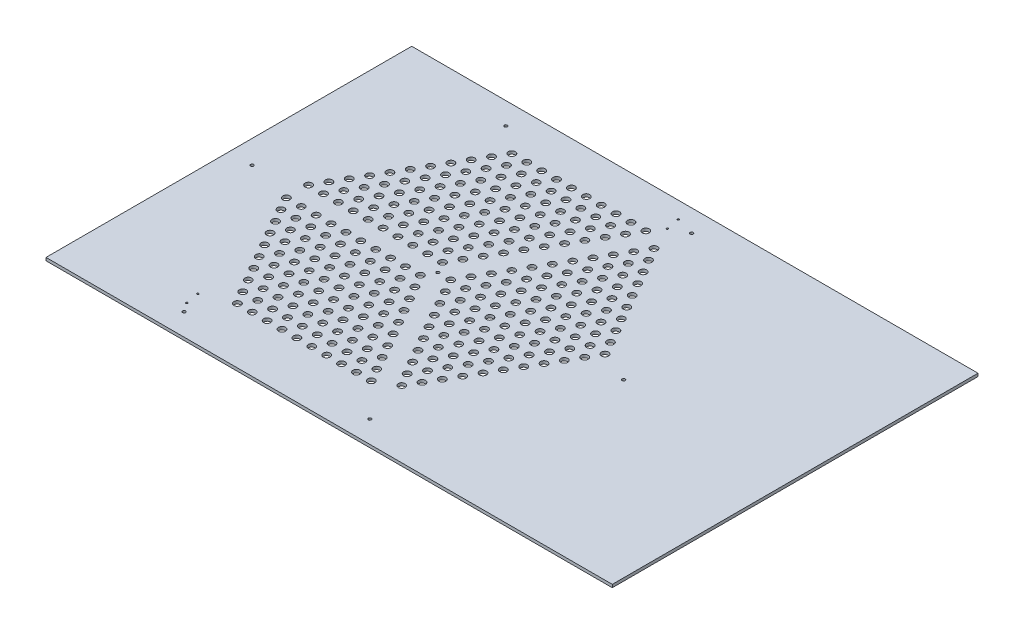
SolidWorks part; units mm, degrees
material "Oak"
ref_plane "Front Plane" through (0, 0, 0) normal (0, 0, 1) x (1, 0, 0)
ref_plane "Top Plane" through (0, 0, 0) normal (0, 1, 0) x (1, 0, 0)
ref_plane "Right Plane" through (0, 0, 0) normal (1, 0, 0) x (0, 0, -1)
sketch "Sketch1" plane through (0, 0, 0) normal (0, 1, 0) x (1, 0, 0)
  line L7 (-450, 393.7) -> (769.2, 393.7)
  line L8 (-450, 393.7) -> (-450, -393.7)
  line L9 (-450, -393.7) -> (769.2, -393.7)
  line L10 (769.2, 393.7) -> (769.2, -393.7)
  point P0 (-450, 0)
  point P3 (-302.9098, 393.7)
  point P6 (-851.5088, 393.7)
  dimension "D1" = 787.4
  dimension "D2" = 1219.2
  dimension "D3" = 450
extrude "Base" add sketch "Sketch1" along normal blind 6.35
sketch "Border Sketch" plane through (0, 6.35, 0) normal (0, 1, 0) x (1, 0, 0)
  line L7 (450, 0) -> (225, 389.7114)
  line L8 (225, 389.7114) -> (-225, 389.7114)
  line L9 (-225, 389.7114) -> (-450, 0)
  line L10 (-450, 0) -> (-225, -389.7114)
  line L11 (-225, -389.7114) -> (225, -389.7114)
  line L12 (225, -389.7114) -> (450, 0)
  line L14 (225, 389.7114) -> (0, 0)
  line L15 (0, 0) -> (225, -389.7114)
  line L20 (-450, 0) -> (0, 0)
  line L21 (0, 5.5) -> (-446.8246, 5.5)
  line L22 (0, -5.5) -> (-446.8246, -5.5)
  line L23 (218.6491, 389.7114) -> (-4.7631, 2.75)
  line L24 (4.7631, -2.75) -> (228.1754, 384.2114)
  line L25 (4.7631, 2.75) -> (228.1754, -384.2114)
  line L26 (-4.7631, -2.75) -> (218.6491, -389.7114)
  circle A0 centre (0, 0) radius 450 construction
  circle A1 centre (0, 0) radius 5.5
  dimension "D1" = 5.5
  dimension "D2" = 5.5
  dimension "D3" = 5.5
  dimension "D4" = 5.5
sketch "Sketch3" plane through (0, 6.35, 0) normal (0, 1, 0) x (1, 0, 0)
  circle A1 centre (27.6379, 0.0396) radius 7.5
  circle A2 centre (43.6579, 27.787) radius 7.5
  circle A3 centre (59.6779, 55.5345) radius 7.5
  circle A4 centre (75.6979, 83.2819) radius 7.5
  circle A5 centre (91.7179, 111.0294) radius 7.5
  circle A6 centre (107.7379, 138.7768) radius 7.5
  circle A7 centre (123.7579, 166.5243) radius 7.5
  circle A8 centre (139.7779, 194.2717) radius 7.5
  circle A9 centre (155.7979, 222.0192) radius 7.5
  circle A10 centre (171.8179, 249.7666) radius 7.5
  circle A11 centre (187.8379, 277.5141) radius 7.5
  circle A12 centre (59.6779, 0.0396) radius 7.5
  circle A13 centre (75.6979, 27.787) radius 7.5
  circle A14 centre (91.7179, 55.5345) radius 7.5
  circle A15 centre (107.7379, 83.2819) radius 7.5
  circle A16 centre (123.7579, 111.0294) radius 7.5
  circle A17 centre (139.7779, 138.7768) radius 7.5
  circle A18 centre (155.7979, 166.5243) radius 7.5
  circle A19 centre (171.8179, 194.2717) radius 7.5
  circle A20 centre (187.8379, 222.0192) radius 7.5
  circle A21 centre (203.8579, 249.7666) radius 7.5
  circle A22 centre (75.6979, -27.7079) radius 7.5
  circle A23 centre (91.7179, 0.0396) radius 7.5
  circle A24 centre (107.7379, 27.787) radius 7.5
  circle A25 centre (123.7579, 55.5345) radius 7.5
  circle A26 centre (139.7779, 83.2819) radius 7.5
  circle A27 centre (155.7979, 111.0294) radius 7.5
  circle A28 centre (171.8179, 138.7768) radius 7.5
  circle A29 centre (187.8379, 166.5243) radius 7.5
  circle A30 centre (203.8579, 194.2717) radius 7.5
  circle A31 centre (219.8779, 222.0192) radius 7.5
  circle A32 centre (91.7179, -55.4553) radius 7.5
  circle A33 centre (107.7379, -27.7079) radius 7.5
  circle A34 centre (123.7579, 0.0396) radius 7.5
  circle A35 centre (139.7779, 27.787) radius 7.5
  circle A36 centre (155.7979, 55.5345) radius 7.5
  circle A37 centre (171.8179, 83.2819) radius 7.5
  circle A38 centre (187.8379, 111.0294) radius 7.5
  circle A39 centre (203.8579, 138.7768) radius 7.5
  circle A40 centre (219.8779, 166.5243) radius 7.5
  circle A41 centre (235.8979, 194.2717) radius 7.5
  circle A42 centre (107.7379, -83.2028) radius 7.5
  circle A43 centre (123.7579, -55.4553) radius 7.5
  circle A44 centre (139.7779, -27.7079) radius 7.5
  circle A45 centre (155.7979, 0.0396) radius 7.5
  circle A46 centre (171.8179, 27.787) radius 7.5
  circle A47 centre (187.8379, 55.5345) radius 7.5
  circle A48 centre (203.8579, 83.2819) radius 7.5
  circle A49 centre (219.8779, 111.0294) radius 7.5
  circle A50 centre (235.8979, 138.7768) radius 7.5
  circle A51 centre (251.9179, 166.5243) radius 7.5
  circle A52 centre (123.7579, -110.9503) radius 7.5
  circle A53 centre (139.7779, -83.2028) radius 7.5
  circle A54 centre (155.7979, -55.4553) radius 7.5
  circle A55 centre (171.8179, -27.7079) radius 7.5
  circle A56 centre (187.8379, 0.0396) radius 7.5
  circle A57 centre (203.8579, 27.787) radius 7.5
  circle A58 centre (219.8779, 55.5345) radius 7.5
  circle A59 centre (235.8979, 83.2819) radius 7.5
  circle A60 centre (251.9179, 111.0294) radius 7.5
  circle A61 centre (267.9379, 138.7768) radius 7.5
  circle A62 centre (139.7779, -138.6977) radius 7.5
  circle A63 centre (155.7979, -110.9503) radius 7.5
  circle A64 centre (171.8179, -83.2028) radius 7.5
  circle A65 centre (187.8379, -55.4553) radius 7.5
  circle A66 centre (203.8579, -27.7079) radius 7.5
  circle A67 centre (219.8779, 0.0396) radius 7.5
  circle A68 centre (235.8979, 27.787) radius 7.5
  circle A69 centre (251.9179, 55.5345) radius 7.5
  circle A70 centre (267.9379, 83.2819) radius 7.5
  circle A71 centre (283.9579, 111.0294) radius 7.5
  circle A72 centre (155.7979, -166.4452) radius 7.5
  circle A73 centre (171.8179, -138.6977) radius 7.5
  circle A74 centre (187.8379, -110.9503) radius 7.5
  circle A75 centre (203.8579, -83.2028) radius 7.5
  circle A76 centre (219.8779, -55.4553) radius 7.5
  circle A77 centre (235.8979, -27.7079) radius 7.5
  circle A78 centre (251.9179, 0.0396) radius 7.5
  circle A79 centre (267.9379, 27.787) radius 7.5
  circle A80 centre (283.9579, 55.5345) radius 7.5
  circle A81 centre (299.9779, 83.2819) radius 7.5
  circle A82 centre (171.8179, -194.1926) radius 7.5
  circle A83 centre (187.8379, -166.4452) radius 7.5
  circle A84 centre (203.8579, -138.6977) radius 7.5
  circle A85 centre (219.8779, -110.9503) radius 7.5
  circle A86 centre (235.8979, -83.2028) radius 7.5
  circle A87 centre (251.9179, -55.4553) radius 7.5
  circle A88 centre (267.9379, -27.7079) radius 7.5
  circle A89 centre (283.9579, 0.0396) radius 7.5
  circle A90 centre (299.9779, 27.787) radius 7.5
  circle A91 centre (315.9979, 55.5345) radius 7.5
  circle A92 centre (187.8379, -221.9401) radius 7.5
  circle A93 centre (203.8579, -194.1926) radius 7.5
  circle A94 centre (219.8779, -166.4452) radius 7.5
  circle A95 centre (235.8979, -138.6977) radius 7.5
  circle A96 centre (251.9179, -110.9503) radius 7.5
  circle A97 centre (267.9379, -83.2028) radius 7.5
  circle A98 centre (283.9579, -55.4553) radius 7.5
  circle A99 centre (299.9779, -27.7079) radius 7.5
  circle A100 centre (315.9979, 0.0396) radius 7.5
  circle A101 centre (332.0179, 27.787) radius 7.5
  circle A102 centre (43.6579, -27.7079) radius 7.5
  circle A103 centre (59.6779, -55.4553) radius 7.5
  circle A104 centre (75.6979, -83.2028) radius 7.5
  circle A105 centre (91.7179, -110.9503) radius 7.5
  circle A106 centre (107.7379, -138.6977) radius 7.5
  circle A107 centre (123.7579, -166.4452) radius 7.5
  circle A108 centre (139.7779, -194.1926) radius 7.5
  circle A109 centre (155.7979, -221.9401) radius 7.5
  circle A110 centre (171.8179, -249.6875) radius 7.5
  circle A111 centre (-13.8596, -23.9117) radius 7.5
  circle A112 centre (-45.8996, -23.9117) radius 7.5
  circle A113 centre (-77.9396, -23.9117) radius 7.5
  circle A114 centre (-109.9796, -23.9117) radius 7.5
  circle A115 centre (-142.0196, -23.9117) radius 7.5
  circle A116 centre (-174.0596, -23.9117) radius 7.5
  circle A117 centre (-206.0996, -23.9117) radius 7.5
  circle A118 centre (-238.1396, -23.9117) radius 7.5
  circle A119 centre (-270.1796, -23.9117) radius 7.5
  circle A120 centre (-302.2196, -23.9117) radius 7.5
  circle A121 centre (-29.8796, -51.6591) radius 7.5
  circle A122 centre (-61.9196, -51.6591) radius 7.5
  circle A123 centre (-93.9596, -51.6591) radius 7.5
  circle A124 centre (-125.9996, -51.6591) radius 7.5
  circle A125 centre (-158.0396, -51.6591) radius 7.5
  circle A126 centre (-190.0796, -51.6591) radius 7.5
  circle A127 centre (-222.1196, -51.6591) radius 7.5
  circle A128 centre (-254.1596, -51.6591) radius 7.5
  circle A129 centre (-286.1996, -51.6591) radius 7.5
  circle A130 centre (-13.8596, -79.4066) radius 7.5
  circle A131 centre (-45.8996, -79.4066) radius 7.5
  circle A132 centre (-77.9396, -79.4066) radius 7.5
  circle A133 centre (-109.9796, -79.4066) radius 7.5
  circle A134 centre (-142.0196, -79.4066) radius 7.5
  circle A135 centre (-174.0596, -79.4066) radius 7.5
  circle A136 centre (-206.0996, -79.4066) radius 7.5
  circle A137 centre (-238.1396, -79.4066) radius 7.5
  circle A138 centre (-270.1796, -79.4066) radius 7.5
  circle A139 centre (2.1604, -107.154) radius 7.5
  circle A140 centre (-29.8796, -107.154) radius 7.5
  circle A141 centre (-61.9196, -107.154) radius 7.5
  circle A142 centre (-93.9596, -107.154) radius 7.5
  circle A143 centre (-125.9996, -107.154) radius 7.5
  circle A144 centre (-158.0396, -107.154) radius 7.5
  circle A145 centre (-190.0796, -107.154) radius 7.5
  circle A146 centre (-222.1196, -107.154) radius 7.5
  circle A147 centre (-254.1596, -107.154) radius 7.5
  circle A148 centre (18.1804, -134.9015) radius 7.5
  circle A149 centre (-13.8596, -134.9015) radius 7.5
  circle A150 centre (-45.8996, -134.9015) radius 7.5
  circle A151 centre (-77.9396, -134.9015) radius 7.5
  circle A152 centre (-109.9796, -134.9015) radius 7.5
  circle A153 centre (-142.0196, -134.9015) radius 7.5
  circle A154 centre (-174.0596, -134.9015) radius 7.5
  circle A155 centre (-206.0996, -134.9015) radius 7.5
  circle A156 centre (-238.1396, -134.9015) radius 7.5
  circle A157 centre (34.2004, -162.649) radius 7.5
  circle A158 centre (2.1604, -162.649) radius 7.5
  circle A159 centre (-29.8796, -162.649) radius 7.5
  circle A160 centre (-61.9196, -162.649) radius 7.5
  circle A161 centre (-93.9596, -162.649) radius 7.5
  circle A162 centre (-125.9996, -162.649) radius 7.5
  circle A163 centre (-158.0396, -162.649) radius 7.5
  circle A164 centre (-190.0796, -162.649) radius 7.5
  circle A165 centre (-222.1196, -162.649) radius 7.5
  circle A166 centre (50.2204, -190.3964) radius 7.5
  circle A167 centre (18.1804, -190.3964) radius 7.5
  circle A168 centre (-13.8596, -190.3964) radius 7.5
  circle A169 centre (-45.8996, -190.3964) radius 7.5
  circle A170 centre (-77.9396, -190.3964) radius 7.5
  circle A171 centre (-109.9796, -190.3964) radius 7.5
  circle A172 centre (-142.0196, -190.3964) radius 7.5
  circle A173 centre (-174.0596, -190.3964) radius 7.5
  circle A174 centre (-206.0996, -190.3964) radius 7.5
  circle A175 centre (66.2404, -218.1439) radius 7.5
  circle A176 centre (34.2004, -218.1439) radius 7.5
  circle A177 centre (2.1604, -218.1439) radius 7.5
  circle A178 centre (-29.8796, -218.1439) radius 7.5
  circle A179 centre (-61.9196, -218.1439) radius 7.5
  circle A180 centre (-93.9596, -218.1439) radius 7.5
  circle A181 centre (-125.9996, -218.1439) radius 7.5
  circle A182 centre (-158.0396, -218.1439) radius 7.5
  circle A183 centre (-190.0796, -218.1439) radius 7.5
  circle A184 centre (82.2604, -245.8913) radius 7.5
  circle A185 centre (50.2204, -245.8913) radius 7.5
  circle A186 centre (18.1804, -245.8913) radius 7.5
  circle A187 centre (-13.8596, -245.8913) radius 7.5
  circle A188 centre (-45.8996, -245.8913) radius 7.5
  circle A189 centre (-77.9396, -245.8913) radius 7.5
  circle A190 centre (-109.9796, -245.8913) radius 7.5
  circle A191 centre (-142.0196, -245.8913) radius 7.5
  circle A192 centre (-174.0596, -245.8913) radius 7.5
  circle A193 centre (98.2804, -273.6388) radius 7.5
  circle A194 centre (66.2404, -273.6388) radius 7.5
  circle A195 centre (34.2004, -273.6388) radius 7.5
  circle A196 centre (2.1604, -273.6388) radius 7.5
  circle A197 centre (-29.8796, -273.6388) radius 7.5
  circle A198 centre (-61.9196, -273.6388) radius 7.5
  circle A199 centre (-93.9596, -273.6388) radius 7.5
  circle A200 centre (-125.9996, -273.6388) radius 7.5
  circle A201 centre (-158.0396, -273.6388) radius 7.5
  circle A202 centre (2.1604, -51.6591) radius 7.5
  circle A203 centre (18.1804, -79.4066) radius 7.5
  circle A204 centre (34.2004, -107.154) radius 7.5
  circle A205 centre (50.2204, -134.9015) radius 7.5
  circle A206 centre (66.2404, -162.649) radius 7.5
  circle A207 centre (82.2604, -190.3964) radius 7.5
  circle A208 centre (98.2804, -218.1439) radius 7.5
  circle A209 centre (114.3004, -245.8913) radius 7.5
  circle A210 centre (130.3204, -273.6388) radius 7.5
  circle A211 centre (-13.8532, 23.9154) radius 7.5
  circle A212 centre (2.1668, 51.6628) radius 7.5
  circle A213 centre (18.1868, 79.4103) radius 7.5
  circle A214 centre (34.2068, 107.1577) radius 7.5
  circle A215 centre (50.2268, 134.9052) radius 7.5
  circle A216 centre (66.2468, 162.6526) radius 7.5
  circle A217 centre (82.2668, 190.4001) radius 7.5
  circle A218 centre (98.2868, 218.1475) radius 7.5
  circle A219 centre (114.3068, 245.895) radius 7.5
  circle A220 centre (130.3268, 273.6425) radius 7.5
  circle A221 centre (146.3468, 301.3899) radius 7.5
  circle A222 centre (-29.8732, 51.6628) radius 7.5
  circle A223 centre (-13.8532, 79.4103) radius 7.5
  circle A224 centre (2.1668, 107.1577) radius 7.5
  circle A225 centre (18.1868, 134.9052) radius 7.5
  circle A226 centre (34.2068, 162.6526) radius 7.5
  circle A227 centre (50.2268, 190.4001) radius 7.5
  circle A228 centre (66.2468, 218.1475) radius 7.5
  circle A229 centre (82.2668, 245.895) radius 7.5
  circle A230 centre (98.2868, 273.6425) radius 7.5
  circle A231 centre (114.3068, 301.3899) radius 7.5
  circle A232 centre (-61.9132, 51.6628) radius 7.5
  circle A233 centre (-45.8932, 79.4103) radius 7.5
  circle A234 centre (-29.8732, 107.1577) radius 7.5
  circle A235 centre (-13.8532, 134.9052) radius 7.5
  circle A236 centre (2.1668, 162.6526) radius 7.5
  circle A237 centre (18.1868, 190.4001) radius 7.5
  circle A238 centre (34.2068, 218.1475) radius 7.5
  circle A239 centre (50.2268, 245.895) radius 7.5
  circle A240 centre (66.2468, 273.6425) radius 7.5
  circle A241 centre (82.2668, 301.3899) radius 7.5
  circle A242 centre (-93.9532, 51.6628) radius 7.5
  circle A243 centre (-77.9332, 79.4103) radius 7.5
  circle A244 centre (-61.9132, 107.1577) radius 7.5
  circle A245 centre (-45.8932, 134.9052) radius 7.5
  circle A246 centre (-29.8732, 162.6526) radius 7.5
  circle A247 centre (-13.8532, 190.4001) radius 7.5
  circle A248 centre (2.1668, 218.1475) radius 7.5
  circle A249 centre (18.1868, 245.895) radius 7.5
  circle A250 centre (34.2068, 273.6425) radius 7.5
  circle A251 centre (50.2268, 301.3899) radius 7.5
  circle A252 centre (-125.9932, 51.6628) radius 7.5
  circle A253 centre (-109.9732, 79.4103) radius 7.5
  circle A254 centre (-93.9532, 107.1577) radius 7.5
  circle A255 centre (-77.9332, 134.9052) radius 7.5
  circle A256 centre (-61.9132, 162.6526) radius 7.5
  circle A257 centre (-45.8932, 190.4001) radius 7.5
  circle A258 centre (-29.8732, 218.1475) radius 7.5
  circle A259 centre (-13.8532, 245.895) radius 7.5
  circle A260 centre (2.1668, 273.6425) radius 7.5
  circle A261 centre (18.1868, 301.3899) radius 7.5
  circle A262 centre (-158.0332, 51.6628) radius 7.5
  circle A263 centre (-142.0132, 79.4103) radius 7.5
  circle A264 centre (-125.9932, 107.1577) radius 7.5
  circle A265 centre (-109.9732, 134.9052) radius 7.5
  circle A266 centre (-93.9532, 162.6526) radius 7.5
  circle A267 centre (-77.9332, 190.4001) radius 7.5
  circle A268 centre (-61.9132, 218.1475) radius 7.5
  circle A269 centre (-45.8932, 245.895) radius 7.5
  circle A270 centre (-29.8732, 273.6425) radius 7.5
  circle A271 centre (-13.8532, 301.3899) radius 7.5
  circle A272 centre (-190.0732, 51.6628) radius 7.5
  circle A273 centre (-174.0532, 79.4103) radius 7.5
  circle A274 centre (-158.0332, 107.1577) radius 7.5
  circle A275 centre (-142.0132, 134.9052) radius 7.5
  circle A276 centre (-125.9932, 162.6526) radius 7.5
  circle A277 centre (-109.9732, 190.4001) radius 7.5
  circle A278 centre (-93.9532, 218.1475) radius 7.5
  circle A279 centre (-77.9332, 245.895) radius 7.5
  circle A280 centre (-61.9132, 273.6425) radius 7.5
  circle A281 centre (-45.8932, 301.3899) radius 7.5
  circle A282 centre (-222.1132, 51.6628) radius 7.5
  circle A283 centre (-206.0932, 79.4103) radius 7.5
  circle A284 centre (-190.0732, 107.1577) radius 7.5
  circle A285 centre (-174.0532, 134.9052) radius 7.5
  circle A286 centre (-158.0332, 162.6526) radius 7.5
  circle A287 centre (-142.0132, 190.4001) radius 7.5
  circle A288 centre (-125.9932, 218.1475) radius 7.5
  circle A289 centre (-109.9732, 245.895) radius 7.5
  circle A290 centre (-93.9532, 273.6425) radius 7.5
  circle A291 centre (-77.9332, 301.3899) radius 7.5
  circle A292 centre (-254.1532, 51.6628) radius 7.5
  circle A293 centre (-238.1332, 79.4103) radius 7.5
  circle A294 centre (-222.1132, 107.1577) radius 7.5
  circle A295 centre (-206.0932, 134.9052) radius 7.5
  circle A296 centre (-190.0732, 162.6526) radius 7.5
  circle A297 centre (-174.0532, 190.4001) radius 7.5
  circle A298 centre (-158.0332, 218.1475) radius 7.5
  circle A299 centre (-142.0132, 245.895) radius 7.5
  circle A300 centre (-125.9932, 273.6425) radius 7.5
  circle A301 centre (-109.9732, 301.3899) radius 7.5
  circle A302 centre (-286.1932, 51.6628) radius 7.5
  circle A303 centre (-270.1732, 79.4103) radius 7.5
  circle A304 centre (-254.1532, 107.1577) radius 7.5
  circle A305 centre (-238.1332, 134.9052) radius 7.5
  circle A306 centre (-222.1132, 162.6526) radius 7.5
  circle A307 centre (-206.0932, 190.4001) radius 7.5
  circle A308 centre (-190.0732, 218.1475) radius 7.5
  circle A309 centre (-174.0532, 245.895) radius 7.5
  circle A310 centre (-158.0332, 273.6425) radius 7.5
  circle A311 centre (-142.0132, 301.3899) radius 7.5
  circle A312 centre (-45.8932, 23.9154) radius 7.5
  circle A313 centre (-77.9332, 23.9154) radius 7.5
  circle A314 centre (-109.9732, 23.9154) radius 7.5
  circle A315 centre (-142.0132, 23.9154) radius 7.5
  circle A316 centre (-174.0532, 23.9154) radius 7.5
  circle A317 centre (-206.0932, 23.9154) radius 7.5
  circle A318 centre (-238.1332, 23.9154) radius 7.5
  circle A319 centre (-270.1732, 23.9154) radius 7.5
  circle A320 centre (-302.2132, 23.9154) radius 7.5
  dimension "D1" = 11
  dimension "D3" = 10
  dimension "D5" = 11
  dimension "D2" = 10
  dimension "D4" = 10
  dimension "D6" = 10
extrude "Cut-Extrude1" cut sketch "Sketch3" against normal up to next (6.35 mm away)
hole_wizard "Ø6.5 (6.5) Diameter Hole1" positions "Sketch4" profile "Sketch5" hole size "Ø6.5" standard "ANSI Metric"
sketch "Sketch4" plane through (0, 14.2875, 0) normal (0, 1, 0) x (-0.5, 0, 0.866)
  point P0 (0, 0)
  point P3 (-400, 0)
  point P11 (-200, 346.4102)
  point P12 (200, 346.4102)
  point P13 (400, 0)
  point P14 (200, -346.4102)
  point P15 (-200, -346.4102)
  point P16 (0, 0)
sketch "Sketch5" plane through (0, 14.2875, 0) normal (1, 0, 0) x (0, 0, 1)
  line L0 (0, 0) -> (0, 14.2875)
  line L1 (0, 14.2875) -> (3.25, 14.2875)
  line L2 (3.25, 14.2875) -> (3.25, 0)
  line L3 (3.25, 0) -> (0, 0)
  line L4 (0, -6.35) -> (0, 107.95) construction
  dimension "Thru Hole Dia." = 6.5
  dimension "Thru Hole Depth" = 14.2875
hole_wizard "Ø4.0 (4) Diameter Hole1" positions "Sketch6" profile "Sketch7" hole size "Ø4.0" standard "ANSI Metric"
sketch "Sketch6" plane through (0, 0, 0) normal (0, -1, 0) x (0.5, 0, -0.866)
  point P0 (-389.7627, -21.2724)
  point P3 (-367.5377, -40.3224)
  point P6 (367.5377, -21.2724)
  point P9 (389.7627, -40.3224)
sketch "Sketch7" plane through (-213.3038, 0, 326.9082) normal (1, 0, 0) x (0, 0, -1)
  line L0 (0, 0) -> (0, 6.35)
  line L1 (0, 6.35) -> (2, 6.35)
  line L2 (2, 6.35) -> (2, 0)
  line L3 (2, 0) -> (0, 0)
  line L4 (0, -6.35) -> (0, 107.95) construction
  dimension "Thru Hole Dia." = 4
  dimension "Thru Hole Depth" = 6.35
sketch "Sketch8" plane through (0, 6.35, 0) normal (0, 1, 0) x (1, 0, 0)
  line L0 (769.2, -393.7) -> (769.2, 393.7) construction
  line L1 (433.0127, 0) -> (216.5064, 375)
  line L2 (216.5064, 375) -> (-216.5064, 375)
  line L3 (-216.5064, 375) -> (-433.0127, 0)
  line L4 (-433.0127, 0) -> (-216.5064, -375)
  line L5 (-216.5064, -375) -> (216.5064, -375)
  line L6 (216.5064, -375) -> (433.0127, 0)
  line L7 (-433.0127, 375) -> (433.0127, 375)
  line L8 (-433.0127, 375) -> (-433.0127, -375)
  line L9 (-433.0127, -375) -> (433.0127, -375)
  line L10 (433.0127, 375) -> (433.0127, -375)
  line L11 (524.4899, 351.665) -> (729.4899, 351.665)
  line L12 (524.4899, 351.665) -> (524.4899, -351.665)
  line L13 (524.4899, -351.665) -> (729.4899, -351.665)
  line L14 (729.4899, 351.665) -> (729.4899, -351.665)
  circle A0 centre (-411.6627, -336.9) radius 2
  circle A1 centre (-411.6627, -359.12) radius 2
  circle A2 centre (-392.6127, -336.9) radius 2
  circle A3 centre (-392.6127, -359.12) radius 2
  circle A4 centre (-401.6127, -73.43) radius 2
  circle A5 centre (-420.8627, -84.54) radius 2
  circle A6 centre (-392.0927, -89.92) radius 2
  circle A7 centre (-411.3427, -101.04) radius 2
  circle A8 centre (392.6127, -359.12) radius 2
  circle A9 centre (392.6127, -336.9) radius 2
  circle A10 centre (411.6627, -359.12) radius 2
  circle A11 centre (411.6627, -336.9) radius 2
  circle A12 centre (420.8627, -84.54) radius 2
  circle A13 centre (411.3427, -101.04) radius 2
  circle A14 centre (392.0927, -89.92) radius 2
  circle A15 centre (401.6127, -73.43) radius 2
  circle A16 centre (708.1399, 342.135) radius 2
  circle A17 centre (689.0899, 319.915) radius 2
  circle A18 centre (708.1399, -319.915) radius 2
  circle A19 centre (689.0899, -342.135) radius 2
  point P49 (729.4899, 0)
  point P50 (769.2, 0)
  dimension "D1" = 21.35
  dimension "D5" = 12.15
  dimension "D15" = 9.53
  dimension "D2" = 15.88
  dimension "D3" = 40.4
  dimension "D4" = 38.1
  dimension "D6" = 21.67
  dimension "D7" = 31.4
  dimension "D8" = 40.92
  dimension "D9" = 290.46
  dimension "D10" = 273.96
  dimension "D11" = 301.57
  dimension "D12" = 285.08
  dimension "D13" = 205
  dimension "D14" = 703.33
  dimension "D16" = 21.35
  dimension "D17" = 31.75
  dimension "D18" = 40.4
  dimension "D19" = 9.53
  dimension "D20" = 40.4
  dimension "D21" = 31.75
  dimension "D22" = 21.35
